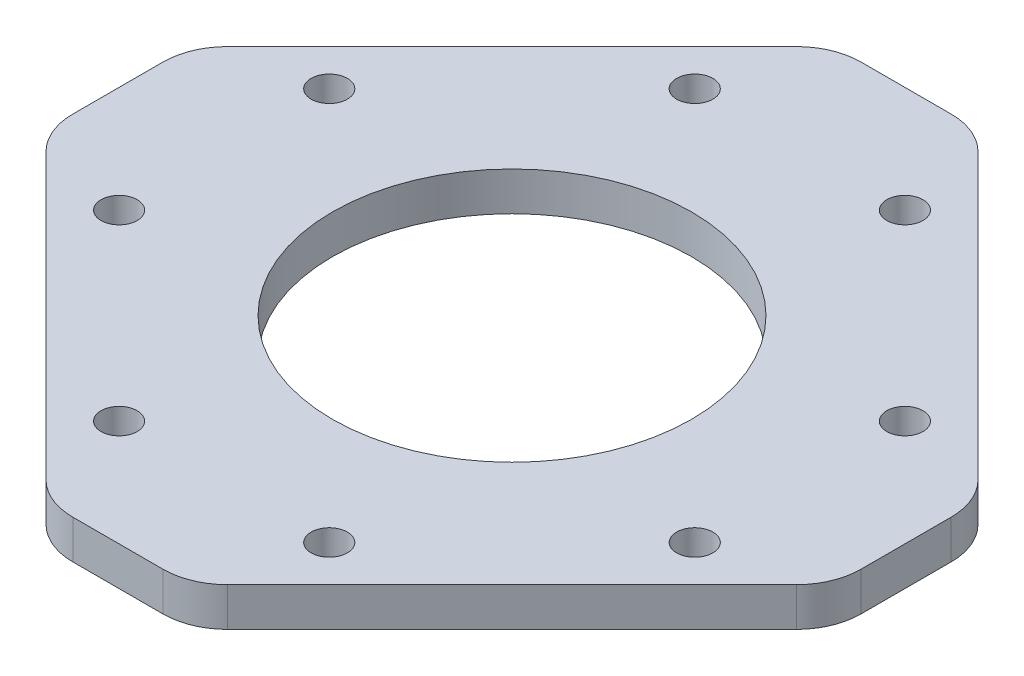
SolidWorks part; units mm, degrees
ref_plane "Front Plane" through (0, 0, 0) normal (0, 0, 1) x (1, 0, 0)
ref_plane "Top Plane" through (0, 0, 0) normal (0, 1, 0) x (1, 0, 0)
ref_plane "Right Plane" through (0, 0, 0) normal (1, 0, 0) x (0, 0, -1)
sketch "Sketch1" plane through (0, 0, 0) normal (0, 1, 0) x (1, 0, 0)
  line L0 (3.4914, 30.5) -> (-3.4914, 30.5)
  line L1 (-7.0269, 29.0355) -> (-29.0355, 7.0269)
  line L2 (-30.5, 3.4914) -> (-30.5, -3.4914)
  line L3 (-29.0355, -7.0269) -> (-7.0269, -29.0355)
  line L4 (-3.4914, -30.5) -> (3.4914, -30.5)
  line L5 (7.0269, -29.0355) -> (29.0355, -7.0269)
  line L6 (30.5, -3.4914) -> (30.5, 3.4914)
  line L7 (29.0355, 7.0269) -> (7.0269, 29.0355)
  arc A0 (7.0269, 29.0355) -> (3.4914, 30.5) centre (3.4914, 25.5) ccw
  arc A1 (-3.4914, 30.5) -> (-7.0269, 29.0355) centre (-3.4914, 25.5) ccw
  arc A2 (-29.0355, 7.0269) -> (-30.5, 3.4914) centre (-25.5, 3.4914) ccw
  arc A3 (-30.5, -3.4914) -> (-29.0355, -7.0269) centre (-25.5, -3.4914) ccw
  arc A4 (-7.0269, -29.0355) -> (-3.4914, -30.5) centre (-3.4914, -25.5) ccw
  arc A5 (3.4914, -30.5) -> (7.0269, -29.0355) centre (3.4914, -25.5) ccw
  arc A6 (29.0355, -7.0269) -> (30.5, -3.4914) centre (25.5, -3.4914) ccw
  arc A7 (30.5, 3.4914) -> (29.0355, 7.0269) centre (25.5, 3.4914) ccw
  circle A8 centre (0, 0) radius 13.9
  circle A9 centre (8.1317, -22.2739) radius 1.4
  circle A10 centre (-8.1317, -22.2739) radius 1.4
  circle A11 centre (-22.2739, -8.1317) radius 1.4
  circle A12 centre (22.2739, -8.1317) radius 1.4
  circle A13 centre (22.2739, 8.1317) radius 1.4
  circle A14 centre (8.1317, 22.2739) radius 1.4
  circle A15 centre (-8.1317, 22.2739) radius 1.4
  circle A16 centre (-22.2739, 8.1317) radius 1.4
  dimension "D2" = 27.8
  dimension "D3" = 2.8
  dimension "D1" = 51
extrude "Boss-Extrude1" add sketch "Sketch1" along normal blind 3
